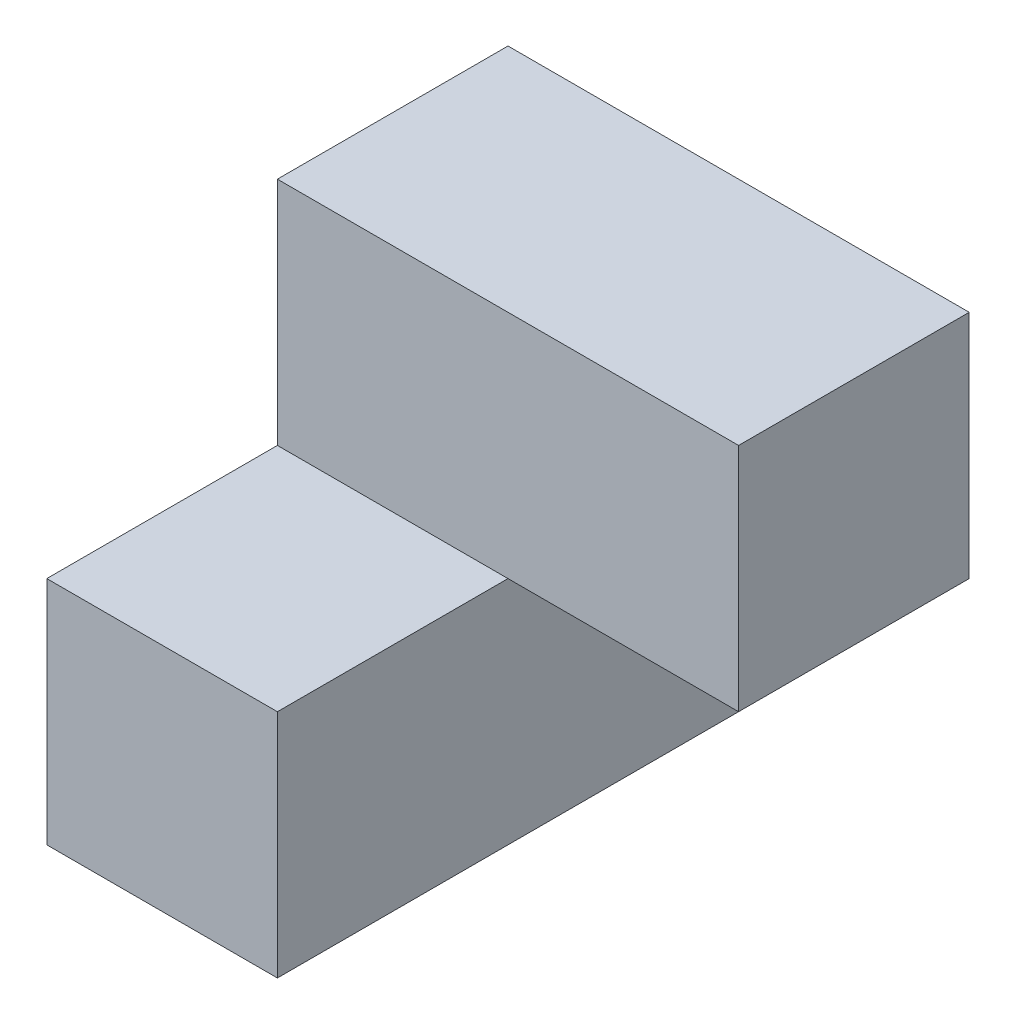
SolidWorks part; units mm, degrees
material "Mahogany"
ref_plane "Front Plane" through (0, 0, 0) normal (0, 0, 1) x (1, 0, 0)
ref_plane "Top Plane" through (0, 0, 0) normal (0, 1, 0) x (1, 0, 0)
ref_plane "Right Plane" through (0, 0, 0) normal (1, 0, 0) x (0, 0, -1)
sketch "Sketch1" plane through (0, 0, 0) normal (0, 1, 0) x (1, 0, 0)
  line L1 (-25.4, -25.4) -> (25.4, -25.4)
  line L2 (-25.4, -25.4) -> (-25.4, 25.4)
  line L3 (-25.4, 25.4) -> (25.4, 25.4)
  line L4 (25.4, -25.4) -> (25.4, 25.4)
  line L5 (-25.4, -25.4) -> (25.4, 25.4) construction
  line L6 (-25.4, 25.4) -> (25.4, -25.4) construction
  point P0 (0, 0)
  dimension "D1" = 50.8
  dimension "D2" = 50.8
extrude "Boss-Extrude1" add sketch "Sketch1" along normal mid plane 50.8
sketch "Sketch2" plane through (0, 25.4, 0) normal (0, 1, 0) x (1, 0, 0)
  line L0 (25.4, -25.4) -> (25.4, 25.4) construction
  line L1 (50.8, -50.8) -> (0, -50.8)
  line L2 (50.8, -50.8) -> (50.8, 0)
  line L3 (50.8, 0) -> (0, 0)
  line L4 (0, -50.8) -> (0, 0)
  line L5 (50.8, -50.8) -> (0, 0) construction
  line L6 (50.8, 0) -> (0, -50.8) construction
  line L7 (-25.4, -25.4) -> (25.4, -25.4) construction
  point P0 (25.4, -25.4)
  dimension "D1" = 25.4
  dimension "D2" = 25.4
extrude "Cut-Extrude1" cut sketch "Sketch2" against normal up to next
sketch "Sketch4" plane through (0, 0, 0) normal (1, 0, 0) x (0, 0, -1)
  line L1 (-25.4, 25.4) -> (0, 25.4)
  line L2 (-25.4, 25.4) -> (-25.4, 0)
  line L3 (-25.4, 0) -> (0, 0)
  line L4 (0, 25.4) -> (0, 0)
extrude "Cut-Extrude2" cut sketch "Sketch4" against normal up to next
sketch "Sketch5" plane through (0, 0, 0) normal (0, 0, 1) x (1, 0, 0)
  line L1 (25.4, -25.4) -> (0, -25.4)
  line L2 (25.4, -25.4) -> (25.4, 0)
  line L3 (25.4, 0) -> (0, 0)
  line L4 (0, -25.4) -> (0, 0)
extrude "Cut-Extrude3" cut sketch "Sketch5" against normal up to next
